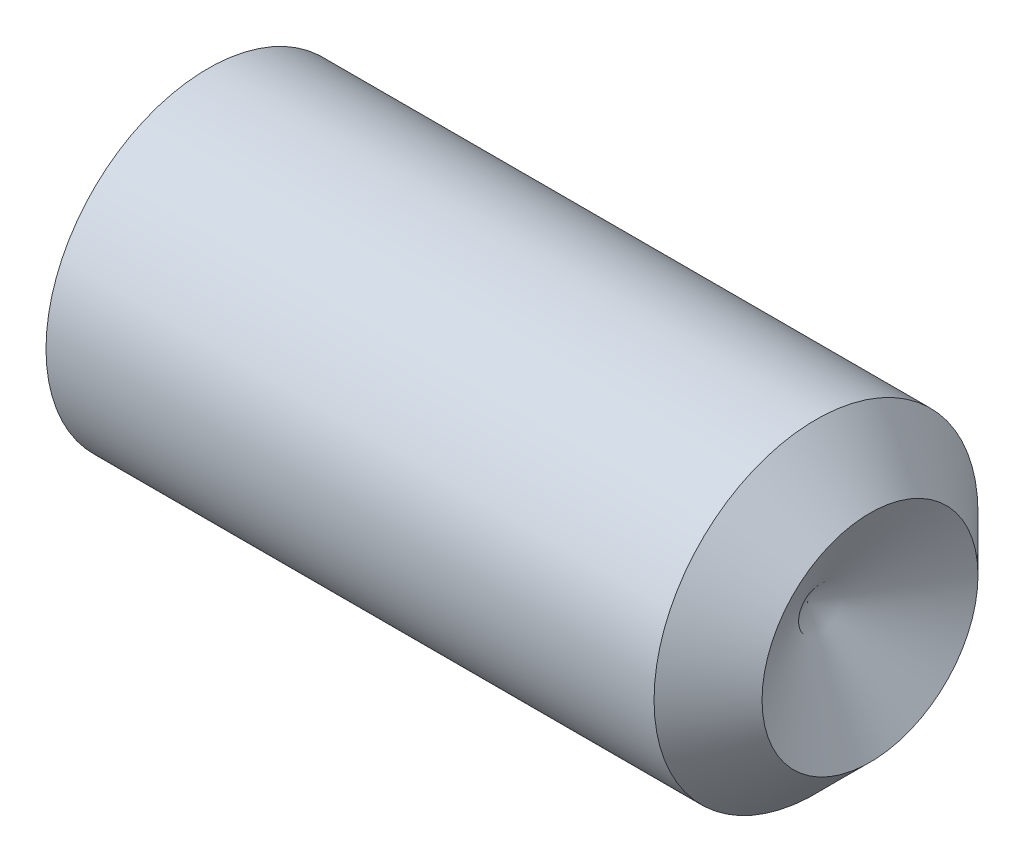
SolidWorks part; units mm, degrees
revolve "BaseBody" add sketch "BodySke" angle 360 about L5
sketch "BodySke" plane through (0, 0, 0) normal (0, 0, 1) x (1, 0, 0)
  line L0 (0, 0) -> (0, 10.352)
  line L1 (0, 10.352) -> (0.9515, 12)
  line L2 (0.9515, 12) -> (46, 12)
  line L3 (46, 12) -> (50, 8)
  line L4 (45.3812, 0) -> (0, 0)
  line L5 (-12.7, 0) -> (88.9, 0) construction
  line L6 (45.3812, 0) -> (50, 8)
  line L7 (50, 8) -> (50, 17.525) construction
  line L8 (0, -10.352) -> (0.9515, -12) construction
  line L9 (45.3812, 0) -> (50, -8) construction
  line L10 (46, -12) -> (50, -8) construction
  line L11 (1.5, 15.875) -> (1.5, -3.175) construction
  dimension "Drive_ch_ang" = 60
  dimension "Cup_ang" = 120
  dimension "Cup_nose_ang" = 45
cosmetic thread "ThreadCosmetic" [suppressed] parameters "Thread_minor"=2.439
ref_plane "Plane1" through (0, 0, 0) normal (0, 0, 1) x (1, 0, 0)
ref_plane "Plane2" through (0, 0, 0) normal (0, 1, 0) x (1, 0, 0)
ref_plane "Plane3" through (0, 0, 0) normal (1, 0, 0) x (0, 0, -1)
sketch "Sketch2" plane through (0, 0, 0) normal (-1, 0, 0) x (0, 0, 1)
  line L0 (3.4641, 6) -> (-3.4641, 6)
  line L1 (-3.4641, 6) -> (-6.9282, 0)
  line L2 (3.4641, 6) -> (6.9282, 0)
  line L3 (3.4641, -6) -> (6.9282, 0)
  line L4 (3.4641, -6) -> (-3.4641, -6)
  line L5 (-3.4641, -6) -> (-6.9282, 0)
  dimension "D2" = 0.75
  dimension "D3" = 0.75
extrude "Hex" cut sketch "Sketch2" against normal blind 15
sketch "ThdSchSke" plane through (0, 0, 0) normal (0, 0, 1) x (1, 0, 0)
  line L0 (0.9515, -10.352) -> (-0.2025, -12)
  line L1 (0.9515, -10.352) -> (2.1054, -12)
  line L2 (2.1054, -12) -> (2.1054, -15)
  line L3 (-3.175, 0) -> (5.1513, 0) construction
  line L4 (0.9515, 12) -> (0.9515, -12) construction
  line L5 (2.1054, -15) -> (-0.2025, -15)
  line L6 (-0.2025, -15) -> (-0.2025, -12)
  dimension "Thread_minor" = 2.439
  dimension "Diameter" = 3
revolve "ThreadSchematic" [suppressed] cut sketch "ThdSchSke" angle 360 about L3
pattern_linear "ThdSchPat" [suppressed]
equation "\"D2@Sketch2\" = \"Hex_size@Sketch2\" / 2"
equation "\"D3@Sketch2\" = \"Hex_size@Sketch2\" / 2"
equation "\"Thread_minor@ThreadCosmetic\" = \"Minor_dia@BodySke\""
equation "\"Thread_minor@ThdSchSke\" = \"Thread_minor@ThreadCosmetic\""
equation "\"Diameter@ThdSchSke\" = \"Diameter@BodySke\""
equation "\"Overcut@ThdSchSke\" = \"Diameter@BodySke\" * 1.25"
equation "\"Num_threads@ThdSchPat\" = int( (\"Length@BodySke\" - ( ( ( \"Diameter@BodySke\" - \"Minor_dia@BodySke\" ) * 0.5 ) / tan( \"Drive_ch_ang@BodySke\" * 0.017453292 ) ) - ( ( ( \"Diameter@BodySke\" - \"Cup_dia@BodySke\" ) * 0.5 ) * tan( \"Cup_nose_ang@BodySke\" * 0.017453292 ) ) ) / \"Advance@BodySke\" + 0.999 )  + 1"
equation "\"Advance@ThdSchPat\" = (\"Length@BodySke\" - ( ( ( \"Diameter@BodySke\" - \"Minor_dia@BodySke\" ) * 0.5 ) / tan( \"Drive_ch_ang@BodySke\" * 0.017453292 ) ) - ( ( ( \"Diameter@BodySke\" - \"Cup_dia@BodySke\" ) * 0.5 ) * tan( \"Cup_nose_ang@BodySke\" * 0.017453292 ) ) ) /  (\"Num_threads@ThdSchPat\" - 1) 'relax it"
equation "' \"Num_threads@ThdSchPat\" = \"Num_threads@ThdSchPat\" - sgn( \"Num_threads@ThdSchPat\" - 1) '---chamfered tips only---"
